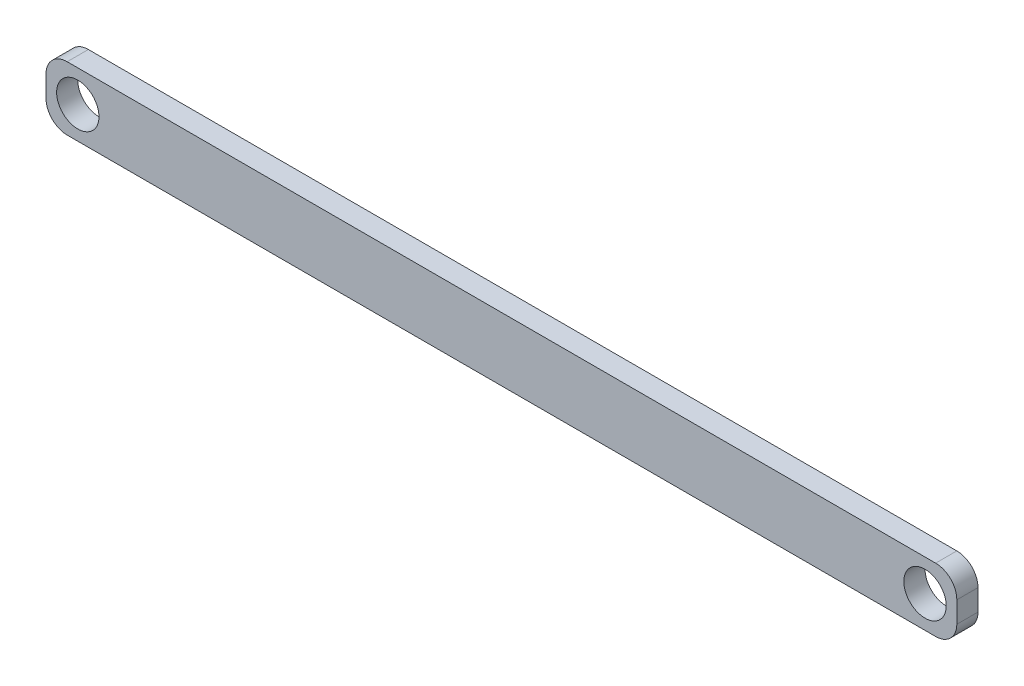
SolidWorks part; units mm, degrees
ref_plane "Alzado" through (0, 0, 0) normal (0, 0, 1) x (1, 0, 0)
ref_plane "Planta" through (0, 0, 0) normal (0, 1, 0) x (1, 0, 0)
ref_plane "Vista lateral" through (0, 0, 0) normal (1, 0, 0) x (0, 0, -1)
sketch "Croquis1" plane through (0, 0, 0) normal (0, 0, 1) x (1, 0, 0)
  line L1 (-205, 15) -> (205, 15)
  line L2 (-215, 5) -> (-215, -5)
  line L3 (-205, -15) -> (205, -15)
  line L4 (215, 5) -> (215, -5)
  line L5 (-215, 15) -> (215, -15) construction
  line L6 (-215, -15) -> (215, 15) construction
  arc A0 (205, 15) -> (215, 5) centre (205, 5) cw
  arc A1 (205, -15) -> (215, -5) centre (205, -5) ccw
  arc A2 (-215, -5) -> (-205, -15) centre (-205, -5) ccw
  arc A3 (-205, 15) -> (-215, 5) centre (-205, 5) ccw
  circle A4 centre (-200, 0) radius 10
  circle A5 centre (200, 0) radius 10
  point P0 (0, 0)
  dimension "D1" = 10
  dimension "D2" = 430
  dimension "D3" = 200
  dimension "D4" = 200
extrude "Saliente-Extruir2" add sketch "Croquis1" along normal mid plane 10
